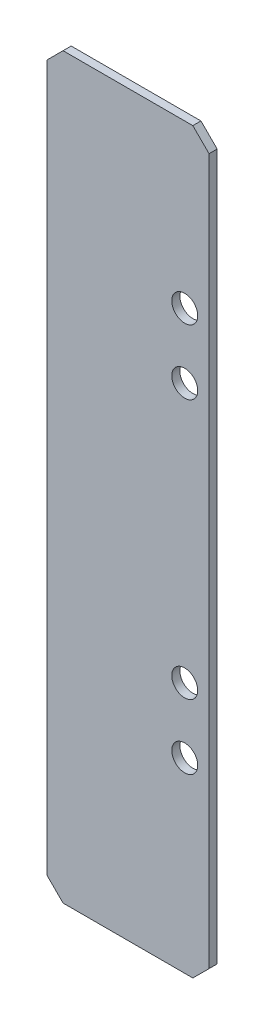
SolidWorks part; units mm, degrees
material "Hexcel AS4C (3000 丝)"
ref_plane "前视基准面" through (0, 0, 0) normal (0, 0, 1) x (1, 0, 0)
ref_plane "上视基准面" through (0, 0, 0) normal (0, 1, 0) x (1, 0, 0)
ref_plane "右视基准面" through (0, 0, 0) normal (1, 0, 0) x (0, 0, -1)
sketch "草图1" plane through (0, 0, 0) normal (0, 0, 1) x (1, 0, 0)
  line L0 (7, 45.5) -> (7, -45.5) construction
  line L1 (-10, 45.5) -> (10, 45.5)
  line L2 (-10, 45.5) -> (-10, -45.5)
  line L3 (-10, -45.5) -> (10, -45.5)
  line L4 (10, 45.5) -> (10, -45.5)
  line L5 (0, -45.5) -> (0, 45.5) construction
  line L6 (-10, 0) -> (10, 0) construction
  line L7 (7, 25.5) -> (7, -14.5) construction
  circle A0 centre (7, 25.5) radius 1.6
  circle A1 centre (7, 17.5) radius 1.6
  circle A2 centre (7, -14.5) radius 1.6
  circle A3 centre (7, -22.5) radius 1.6
  point P0 (0, 0)
  dimension "D4" = 3.2
  dimension "D1" = 91
  dimension "D2" = 20
  dimension "D3" = 3
  dimension "D5" = 8
  dimension "D6" = 20
  dimension "D8" = 40
  dimension "D7" = 2
extrude "凸台-拉伸1" add sketch "草图1" along normal blind 1
chamfer "倒角1" distance 2 angle 45 4 edges at (-10, 45.5, 0.5) (-10, -45.5, 0.5) (10, -45.5, 0.5) (10, 45.5, 0.5)
